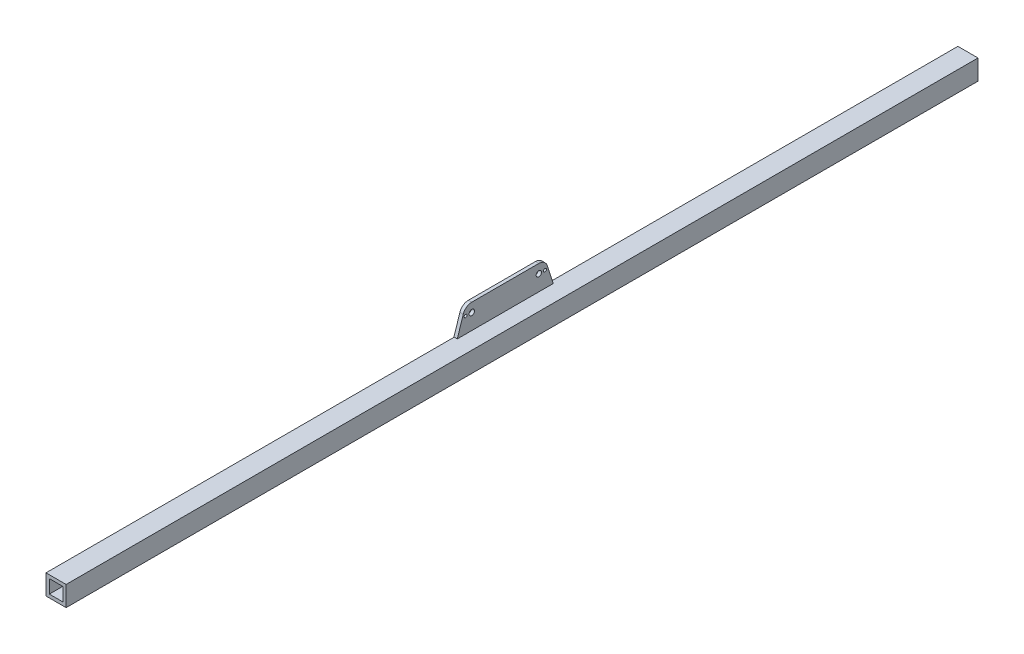
SolidWorks part; units mm, degrees
ref_plane "Front Plane" through (0, 0, 0) normal (0, 0, 1) x (1, 0, 0)
ref_plane "Top Plane" through (0, 0, 0) normal (0, 1, 0) x (1, 0, 0)
ref_plane "Right Plane" through (0, 0, 0) normal (1, 0, 0) x (0, 0, -1)
sketch "Sketch1" plane through (0, 0, 0) normal (0, 0, 1) x (1, 0, 0)
  line L1 (-9.525, -9.525) -> (9.525, -9.525)
  line L2 (-9.525, -9.525) -> (-9.525, 9.525)
  line L3 (-9.525, 9.525) -> (9.525, 9.525)
  line L4 (9.525, -9.525) -> (9.525, 9.525)
  line L5 (-9.525, -9.525) -> (9.525, 9.525) construction
  line L6 (-9.525, 9.525) -> (9.525, -9.525) construction
  point P0 (0, 0)
  dimension "D1" = 19.05
  dimension "D2" = 19.05
extrude "Boss-Extrude1" add sketch "Sketch1" against normal blind 863.6
sketch "Sketch2" plane through (0, 0, 0) normal (0, 0, 1) x (1, 0, 0)
  line L1 (-6.35, -6.35) -> (6.35, -6.35)
  line L2 (-6.35, -6.35) -> (-6.35, 6.35)
  line L3 (-6.35, 6.35) -> (6.35, 6.35)
  line L4 (6.35, -6.35) -> (6.35, 6.35)
  line L5 (-6.35, -6.35) -> (6.35, 6.35) construction
  line L6 (-6.35, 6.35) -> (6.35, -6.35) construction
  point P0 (0, 0)
  dimension "D1" = 12.7
  dimension "D2" = 12.7
extrude "Cut-Extrude1" cut sketch "Sketch2" against normal up to next
sketch "Sketch3" plane through (-9.525, 0, 0) normal (-1, 0, 0) x (0, 0, 1)
  line L0 (-400.05, 33.0855) -> (-463.55, 33.0855) construction
  line L1 (-400.05, 33.0855) -> (-463.55, 33.0855)
  line L2 (-471.6088, 27.2262) -> (-477.2649, 9.7774) construction
  line L3 (-471.6088, 27.2262) -> (-477.2649, 9.7774)
  line L4 (-386.3351, 9.7774) -> (-391.9912, 27.2262) construction
  line L5 (-386.3351, 9.7774) -> (-391.9912, 27.2262)
  line L6 (-477.2649, 9.7774) -> (-386.3351, 9.7774)
  spline S0 degree 3 poles (-559.1102, 5031.6977) (-436.8682, -3.9415) (-450.9649, 33.7655) (-464.1264, 33.0674) (-464.4138, 33.0431) (-464.7002, 33.0087) (-465.0803, 32.9501) (-465.457, 32.872) (-465.8291, 32.7749) (-466.2314, 32.6551) (-466.7503, 32.4678) (-467.3722, 32.1854) (-467.9696, 31.8536) (-468.5375, 31.4726) (-469.074, 31.0496) (-469.7407, 30.4297) (-470.4605, 29.5735) (-470.9557, 28.7555) (-471.2405, 28.1736) (-471.3821, 27.8528) (-476.0002, 15.8677) (-448.3856, -7.2084) (-5203.9946, 1639.3387) knots -3.631082 -3.631082 -3.631082 -3.631082 0.027083 0.054165 0.081248 0.10833 0.135413 0.189578 0.21666 0.243743 0.307821 0.371897 0.436011 0.500107 0.564389 0.628264 0.756365 0.878116 0.896532 0.938874 0.976861 4.513572 4.513572 4.513572 4.513572 only from (-463.55, 33.0855) to (-471.6088, 27.2262) construction
  spline S1 degree 3 poles (-463.55, 33.0855) (-463.6461, 33.0846) (-463.8384, 33.0827) (-464.1264, 33.0674) (-464.4138, 33.0431) (-464.7002, 33.0087) (-465.0803, 32.9501) (-465.457, 32.872) (-465.8291, 32.7749) (-466.2314, 32.6551) (-466.7503, 32.4678) (-467.3722, 32.1854) (-467.9696, 31.8536) (-468.5375, 31.4726) (-469.074, 31.0496) (-469.7407, 30.4297) (-470.4605, 29.5735) (-470.9557, 28.7555) (-471.2405, 28.1736) (-471.3821, 27.8528) (-471.5142, 27.51) (-471.5828, 27.3041) (-471.6088, 27.2262) knots 0 0 0 0 0.027083 0.054165 0.081248 0.10833 0.135413 0.189578 0.21666 0.243743 0.307821 0.371897 0.436011 0.500107 0.564389 0.628264 0.756365 0.878116 0.896532 0.938874 0.976861 1 1 1 1
  spline S2 degree 3 poles (4333.5749, 1659.4886) (-418.9864, -9.573) (-387.4637, 15.4641) (-392.1862, 27.769) (-392.298, 28.0348) (-392.4189, 28.2967) (-392.592, 28.6401) (-392.7824, 28.9745) (-392.9895, 29.2985) (-393.2275, 29.6442) (-393.5657, 30.0801) (-394.0261, 30.5846) (-394.5259, 31.0506) (-395.0635, 31.4733) (-395.6313, 31.8532) (-396.4266, 32.2962) (-397.463, 32.7171) (-398.3939, 32.9359) (-399.0352, 33.0274) (-399.384, 33.0631) (-412.2092, 33.7605) (-425.6456, 0.3758) (-325.7607, 5031.9726) knots -3.631082 -3.631082 -3.631082 -3.631082 0.027083 0.054165 0.081248 0.10833 0.135413 0.189578 0.21666 0.243743 0.307821 0.371897 0.436011 0.500107 0.564389 0.628264 0.756365 0.878116 0.896532 0.938874 0.976861 4.513572 4.513572 4.513572 4.513572 only from (-391.9912, 27.2262) to (-400.05, 33.0855) construction
  spline S3 degree 3 poles (-391.9912, 27.2262) (-392.0218, 27.3174) (-392.0828, 27.4997) (-392.1862, 27.769) (-392.298, 28.0348) (-392.4189, 28.2967) (-392.592, 28.6401) (-392.7824, 28.9745) (-392.9895, 29.2985) (-393.2275, 29.6442) (-393.5657, 30.0801) (-394.0261, 30.5846) (-394.5259, 31.0506) (-395.0635, 31.4733) (-395.6313, 31.8532) (-396.4266, 32.2962) (-397.463, 32.7171) (-398.3939, 32.9359) (-399.0352, 33.0274) (-399.384, 33.0631) (-399.7509, 33.083) (-399.9679, 33.0848) (-400.05, 33.0855) knots 0 0 0 0 0.027083 0.054165 0.081248 0.10833 0.135413 0.189578 0.21666 0.243743 0.307821 0.371897 0.436011 0.500107 0.564389 0.628264 0.756365 0.878116 0.896532 0.938874 0.976861 1 1 1 1
extrude "Boss-Extrude2" add sketch "Sketch3" against normal blind 3.175 separate body
sketch "Sketch5" plane through (-9.525, 0, 0) normal (-1, 0, 0) x (0, 0, 1)
  circle A1 centre (-394.208, 24.6139) radius 1.3671
  circle A2 centre (-394.208, 24.6139) radius 1.3671
  circle A3 centre (-469.392, 24.6139) radius 1.3671
  circle A4 centre (-469.392, 24.6139) radius 1.3671
  circle A5 centre (-400.05, 24.6139) radius 2.5572
  circle A6 centre (-400.05, 24.6139) radius 2.5572
  circle A7 centre (-463.55, 24.6139) radius 2.5576
  circle A8 centre (-463.55, 24.6139) radius 2.5576
  dimension "D1" = 0
  dimension "D2" = 0
  dimension "D3" = 0
  dimension "D4" = 0
extrude "Cut-Extrude2" cut sketch "Sketch5" against normal blind 3.175
equation "\"D2@Sketch1\"=\"D1@Sketch1\""
equation "\"D2@Sketch2\"=\"D1@Sketch2\""
